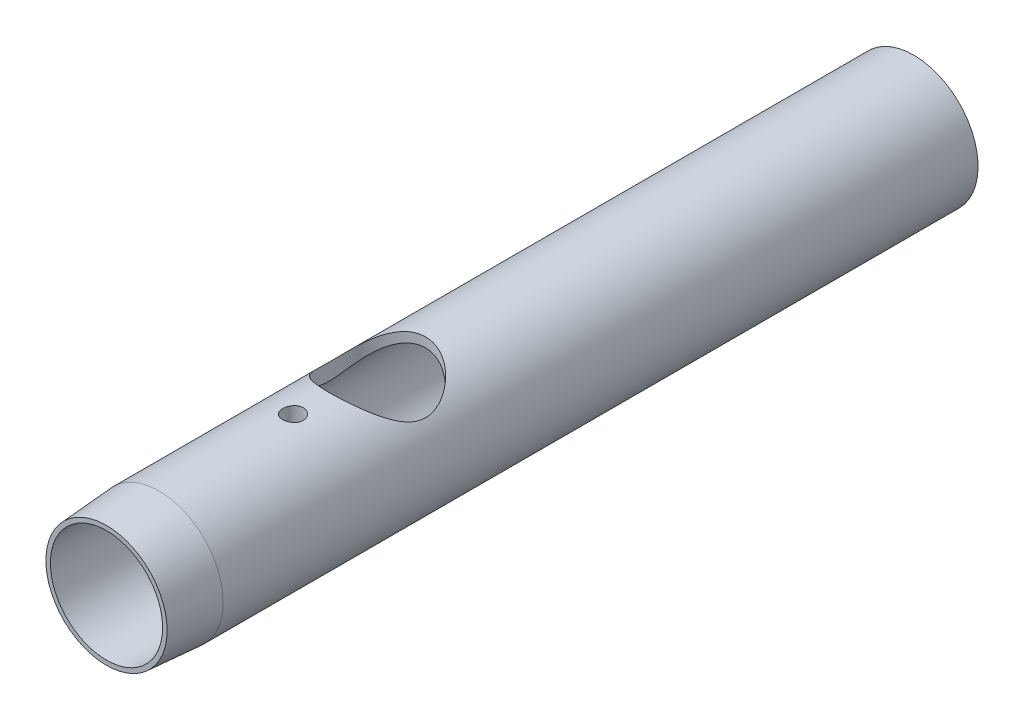
SolidWorks part; units mm, degrees
material "6061 Alloy"
ref_plane "Front Plane" through (0, 0, 0) normal (0, 0, 1) x (1, 0, 0)
ref_plane "Top Plane" through (0, 0, 0) normal (0, 1, 0) x (1, 0, 0)
ref_plane "Right Plane" through (0, 0, 0) normal (1, 0, 0) x (0, 0, -1)
sketch "Sketch1" plane through (0, 0, 0) normal (0, 0, 1) x (1, 0, 0)
  circle A0 centre (0, 0) radius 12.7
extrude "Extrude1" add sketch "Sketch1" along normal blind 159.512
sketch "Sketch3" plane through (0, 0, 0) normal (0, 0, -1) x (-1, 0, 0)
  circle A0 centre (0, 0) radius 10.8204
extrude "Cut-Extrude1" cut sketch "Sketch3" against normal blind 114.808
sketch "Sketch4" plane through (0, 0, 114.808) normal (0, 0, -1) x (-1, 0, 0)
  circle A0 centre (0, 0) radius 9.017
extrude "Cut-Extrude2" cut sketch "Sketch4" against normal through all
chamfer "Chamfer1" distance 1.778 angle 45 1 edges at (-9.017, 0, 114.808)
chamfer "Chamfer2" distance 0.762 distance2 0.508 1 edges at (-9.017, 0, 116.586)
sketch "Sketch5" plane through (0, 0, 159.512) normal (0, 0, 1) x (1, 0, 0)
  circle A0 centre (0, 0) radius 9.5758
extrude "Cut-Extrude3" cut sketch "Sketch5" against normal blind 29.21
sketch "Sketch8" plane through (0, 0, 159.512) normal (0, 0, 1) x (1, 0, 0)
  circle A0 centre (0, 0) radius 10.287
extrude "Cut-Extrude5" cut sketch "Sketch8" against normal blind 25.273
sketch "Sketch9" plane through (0, 0, 159.512) normal (0, 0, 1) x (1, 0, 0)
  circle A0 centre (0, 0) radius 11.0871
extrude "Cut-Extrude6" cut sketch "Sketch9" against normal blind 18.1864
chamfer "Chamfer3" distance 10.3632 distance2 0.7239 1 edges at (12.7, 0, 159.512)
ref_plane "Plane1" through (0, -12.7, 0) normal (0, 1, 0) x (-1, 0, 0)
sketch "Sketch10" plane through (0, -12.7, 0) normal (0, 1, 0) x (-1, 0, 0)
  line L0 (0, -7.0948) -> (0, 102.1514) construction
  line L1 (2.3114, 0) -> (2.3114, 72.0725)
  line L2 (2.3114, 0) -> (-2.3114, 0)
  line L3 (-2.3114, 0) -> (-2.3114, 94.9325)
  line L4 (-0.7239, 96.52) -> (0.1651, 96.52)
  line L5 (3.8989, 73.66) -> (5.4991, 73.66)
  line L6 (7.0866, 75.2475) -> (7.0866, 107.6325)
  line L7 (5.4991, 109.22) -> (3.3401, 109.22)
  line L8 (1.7526, 107.6325) -> (1.7526, 98.1075)
  arc A0 (-2.3114, 94.9325) -> (-0.7239, 96.52) centre (-0.7239, 94.9325) cw
  arc A1 (5.4991, 109.22) -> (7.0866, 107.6325) centre (5.4991, 107.6325) cw
  arc A2 (1.7526, 107.6325) -> (3.3401, 109.22) centre (3.3401, 107.6325) cw
  arc A3 (5.4991, 73.66) -> (7.0866, 75.2475) centre (5.4991, 75.2475) ccw
  arc A4 (2.3114, 72.0725) -> (3.8989, 73.66) centre (3.8989, 72.0725) cw
  arc A5 (0.1651, 96.52) -> (1.7526, 98.1075) centre (0.1651, 98.1075) ccw
  point P5 (0, 86.36)
  point P7 (0, 0)
  dimension "D1" = 1.5875
extrude "Cut-Extrude7" cut sketch "Sketch10" along normal blind 7.62
sketch "Sketch11" plane through (0, -12.7, 0) normal (0, 1, 0) x (-1, 0, 0)
  line L0 (0, 0) -> (0, 126.619)
  circle A1 centre (0, 126.619) radius 2.032
extrude "Cut-Extrude11" cut sketch "Sketch11" along normal blind 3.302
sketch "Sketch15" plane through (0, -9.398, 0) normal (0, -1, 0) x (1, 0, 0)
  circle A0 centre (0, 126.619) radius 1.7018
extrude "Cut-Extrude12" cut sketch "Sketch15" against normal blind 3.302
ref_plane "Plane2" through (0, 12.7, 0) normal (0, 1, 0) x (-1, 0, 0)
sketch "Sketch16" plane through (0, 12.7, 0) normal (0, 1, 0) x (-1, 0, 0)
  line L0 (0, 0) -> (0, 105.9688)
  circle A0 centre (0, 105.9688) radius 9.525
extrude "Cut-Extrude13" cut sketch "Sketch16" against normal blind 12.7
sketch "Sketch17" plane through (0, 12.7, 0) normal (0, 1, 0) x (-1, 0, 0)
  line L0 (0, 0) -> (0, 122.682)
  circle A0 centre (0, 122.682) radius 2.032
extrude "Cut-Extrude14" cut sketch "Sketch17" against normal blind 3.302
sketch "Sketch18" plane through (0, 9.398, 0) normal (0, 1, 0) x (-1, 0, 0)
  circle A0 centre (0, 122.682) radius 1.7018
  point P3 (-20.5275, 108.6779)
extrude "Cut-Extrude15" cut sketch "Sketch18" against normal blind 3.302
